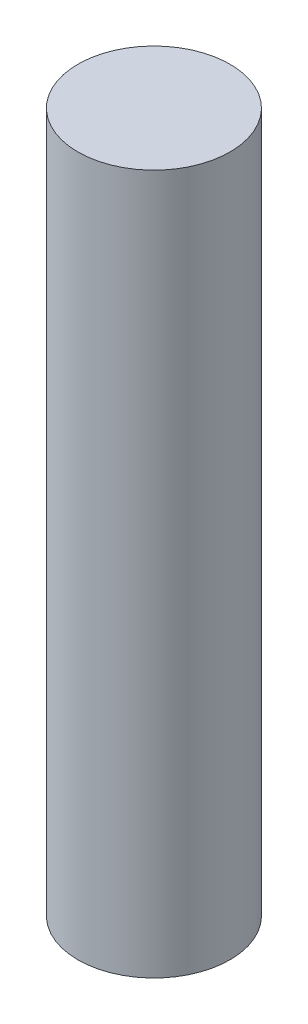
SolidWorks part; units mm, degrees
ref_plane "Front Plane" through (0, 0, 0) normal (0, 0, 1) x (1, 0, 0)
ref_plane "Top Plane" through (0, 0, 0) normal (0, 1, 0) x (1, 0, 0)
ref_plane "Right Plane" through (0, 0, 0) normal (1, 0, 0) x (0, 0, -1)
sketch "Sketch1" plane through (0, 0, 0) normal (0, 1, 0) x (1, 0, 0)
  circle A0 centre (0, 0) radius 2.5
  dimension "D1" = 5
extrude "Boss-Extrude1" add sketch "Sketch1" along normal blind 23
